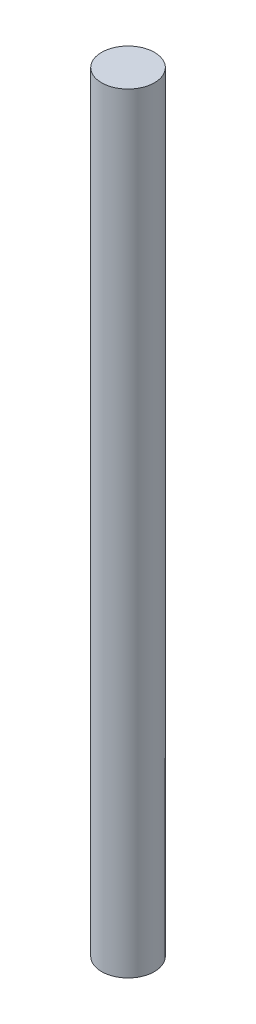
SolidWorks part; units mm, degrees
ref_plane "Front Plane" through (0, 0, 0) normal (0, 0, 1) x (1, 0, 0)
ref_plane "Top Plane" through (0, 0, 0) normal (0, 1, 0) x (1, 0, 0)
ref_plane "Right Plane" through (0, 0, 0) normal (1, 0, 0) x (0, 0, -1)
sketch "Sketch1" plane through (0, 0, 0) normal (1, 0, 0) x (0, 0, -1)
  line L0 (0, -1750) -> (0, 250) construction
  line L1 (0, 0) -> (0, -1750)
revolve "Revolve-Thin3" add sketch "Sketch1" angle 360 about L0 wall 60
